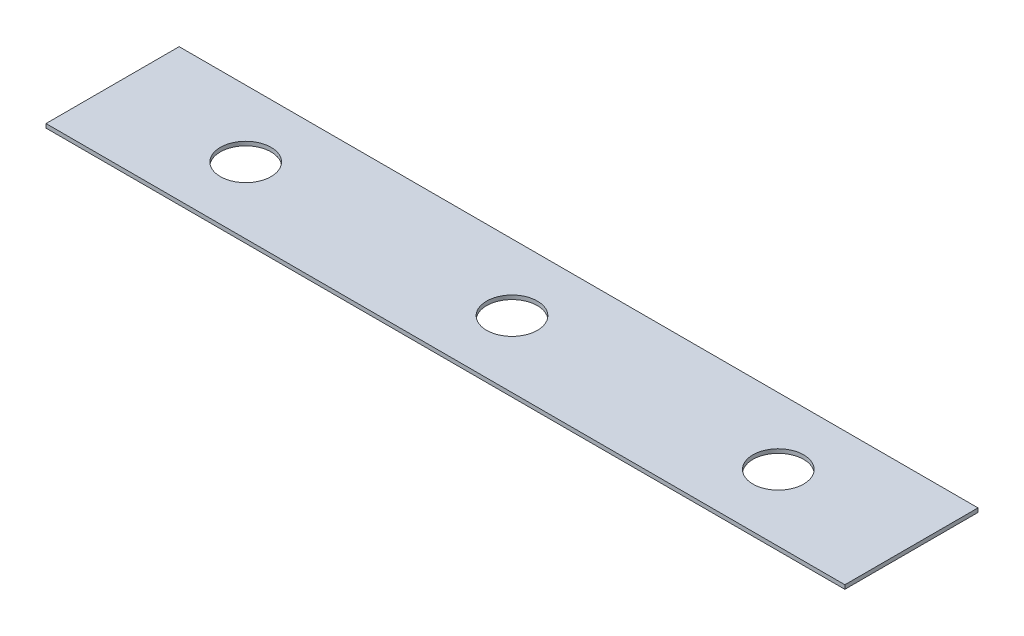
SolidWorks part; units mm, degrees
ref_plane "Front Plane" through (0, 0, 0) normal (0, 0, 1) x (1, 0, 0)
ref_plane "Top Plane" through (0, 0, 0) normal (0, 1, 0) x (1, 0, 0)
ref_plane "Right Plane" through (0, 0, 0) normal (1, 0, 0) x (0, 0, -1)
sketch "Sketch1" plane through (0, 0, 0) normal (0, 1, 0) x (1, 0, 0)
  line L1 (-38.1, 6.35) -> (38.1, 6.35)
  line L2 (-38.1, 6.35) -> (-38.1, -6.35)
  line L3 (-38.1, -6.35) -> (38.1, -6.35)
  line L4 (38.1, 6.35) -> (38.1, -6.35)
  line L5 (-38.1, 6.35) -> (38.1, -6.35) construction
  line L6 (-38.1, -6.35) -> (38.1, 6.35) construction
  point P0 (0, 0)
  dimension "D1" = 12.7
  dimension "D2" = 76.2
extrude "Boss-Extrude1" add sketch "Sketch1" along normal blind 0.381
sketch "Sketch2" plane through (0, 0.381, 0) normal (0, 1, 0) x (1, 0, 0)
  circle A0 centre (0, 0) radius 2.4194
  circle A1 centre (-25.4, 0) radius 2.4193
  circle A2 centre (25.4, 0) radius 2.4193
  dimension "D3" = 4.8387
  dimension "D1" = 25.4
  dimension "D2" = 25.4
extrude "Cut-Extrude1" cut sketch "Sketch2" against normal through all
